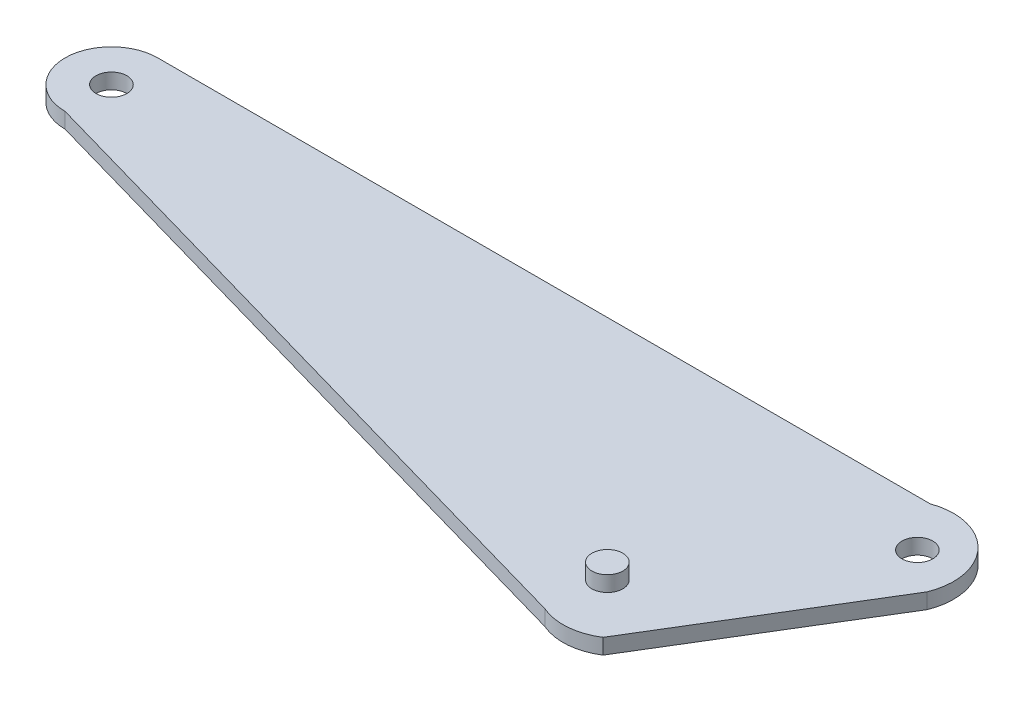
SolidWorks part; units mm, degrees
ref_plane "Front Plane" through (0, 0, 0) normal (0, 0, 1) x (1, 0, 0)
ref_plane "Top Plane" through (0, 0, 0) normal (0, 1, 0) x (1, 0, 0)
ref_plane "Right Plane" through (0, 0, 0) normal (1, 0, 0) x (0, 0, -1)
sketch "Sketch1" plane through (0, 0, 0) normal (0, 1, 0) x (1, 0, 0)
  line L0 (-26.085, 0) -> (26.085, 0)
  line L1 (-26.085, 3) -> (23.915, 3)
  line L2 (-26.085, -3) -> (17.3225, -15.3503)
  line L3 (18.8042, -11.9578) -> (26.085, 0) construction
  line L4 (28.7437, -2.0418) -> (20.8126, -15.0676)
  circle A0 centre (-26.085, 0) radius 1
  circle A1 centre (26.085, 0) radius 1
  circle A2 centre (18.8042, -11.9578) radius 1
  arc A4 (20.8126, -15.0676) -> (17.3225, -15.3503) centre (18.8042, -11.9578) cw
  arc A5 (-26.085, 3) -> (-26.085, -3) centre (-26.085, 0) ccw
  arc A7 (23.915, 3) -> (28.7437, -2.0418) centre (25.2057, -0.597) cw
  point P5 (0, 0)
  dimension "D2" = 2
  dimension "D3" = 2
  dimension "D1" = 52.17
  dimension "D4" = 3
  dimension "D5" = 3
  dimension "D7" = 14
extrude "Boss-Extrude4" add sketch "Sketch1" along normal blind 1
sketch "Sketch4" plane through (0, 1, 0) normal (0, 1, 0) x (1, 0, 0)
  circle A0 centre (17.7327, -11.7153) radius 1
  dimension "D1" = 2
extrude "Boss-Extrude5" add sketch "Sketch4" along normal blind 1
